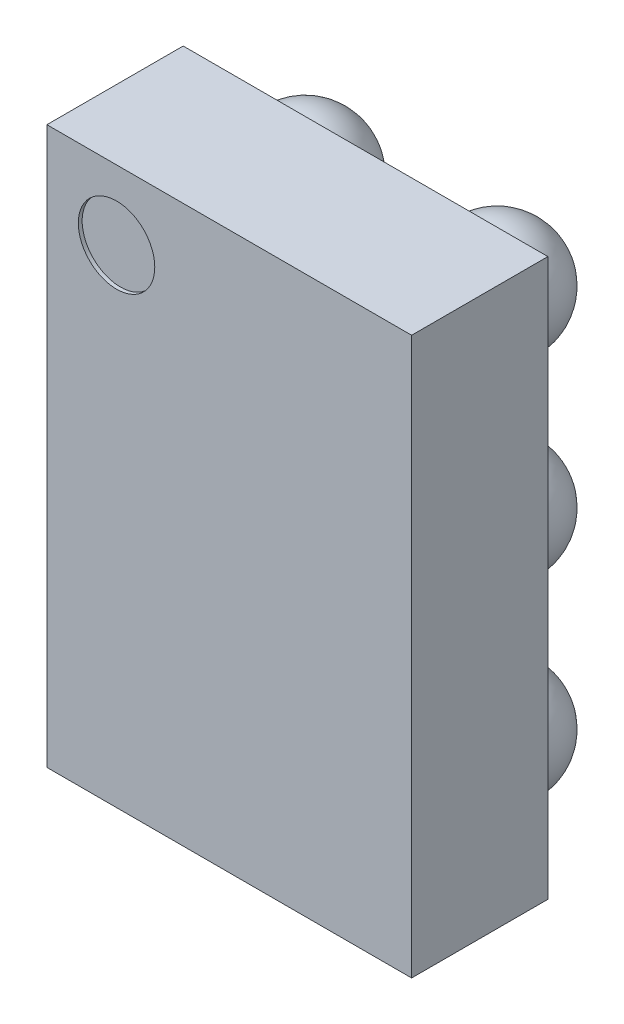
SolidWorks part; units mm, degrees
ref_plane "Front Plane" through (0, 0, 0) normal (0, 0, 1) x (1, 0, 0)
ref_plane "Top Plane" through (0, 0, 0) normal (0, 1, 0) x (1, 0, 0)
ref_plane "Right Plane" through (0, 0, 0) normal (1, 0, 0) x (0, 0, -1)
sketch "Sketch1" plane through (0, 0, 0) normal (0, 0, 1) x (1, 0, 0)
  line L1 (-0.475, -0.725) -> (0.475, -0.725)
  line L2 (-0.475, -0.725) -> (-0.475, 0.725)
  line L3 (-0.475, 0.725) -> (0.475, 0.725)
  line L4 (0.475, -0.725) -> (0.475, 0.725)
  line L5 (-0.475, -0.725) -> (0.475, 0.725) construction
  line L6 (-0.475, 0.725) -> (0.475, -0.725) construction
  point P0 (0, 0)
  dimension "D1" = 0.95
  dimension "D2" = 1.45
extrude "Boss-Extrude1" add sketch "Sketch1" along normal blind 0.355 from offset 0.24
ref_plane "Plane1" through (0.25, 0, 0) normal (1, 0, 0) x (0, 0, -1)
sketch "Sketch2" plane through (0.25, 0, 0) normal (1, 0, 0) x (0, 0, -1)
  line L0 (-0.295, 0.5) -> (0, 0.5)
  arc A0 (-0.295, 0.5) -> (0, 0.5) centre (-0.1475, 0.5) ccw
  dimension "D1" = 0.1475
  dimension "D2" = 0.5
revolve "Revolve1" add sketch "Sketch2" angle 360 about L0
pattern_linear "LPattern1" count 2 spacing 0.5 along (-1, 0, 0) count 3 spacing 0.5 along (0, -1, 0) of "Revolve1"
sketch "Sketch3" plane through (0, 0, 0.595) normal (0, 0, 1) x (1, 0, 0)
  circle A0 centre (-0.2936, 0.5441) radius 0.0996
extrude "Cut-Extrude1" cut sketch "Sketch3" against normal blind 0.01
